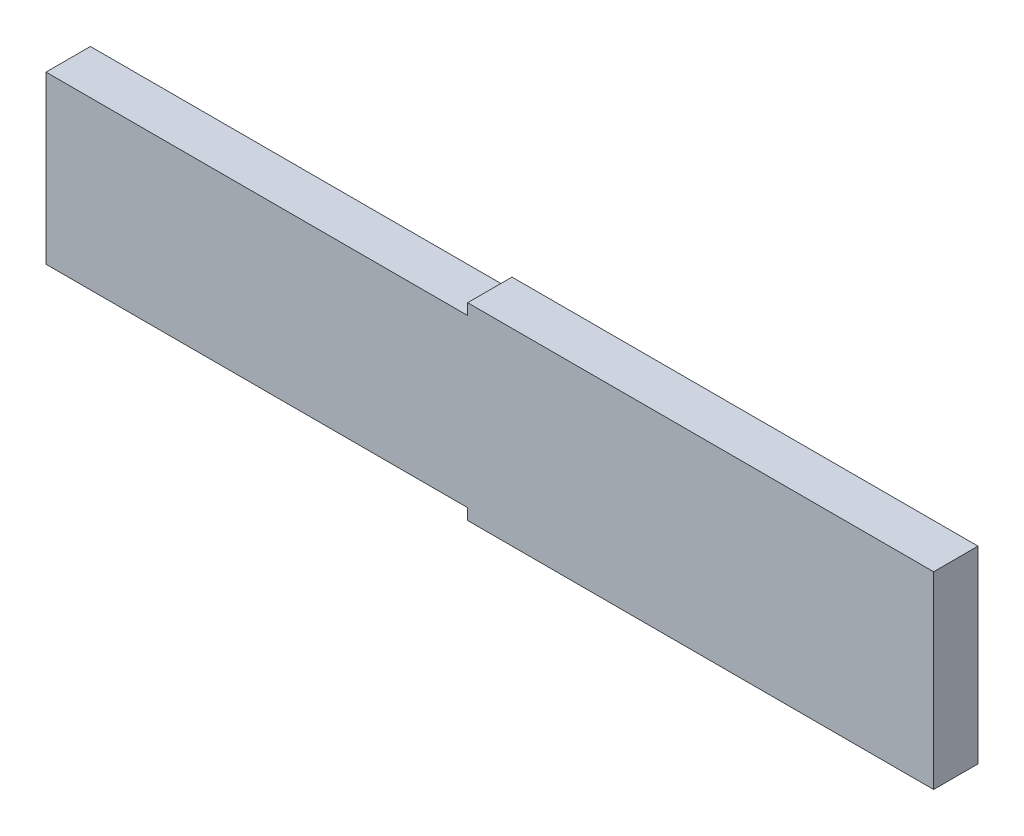
SolidWorks part; units mm, degrees
ref_plane "Ebene vorne" through (0, 0, 0) normal (0, 0, 1) x (1, 0, 0)
ref_plane "Ebene oben" through (0, 0, 0) normal (0, 1, 0) x (1, 0, 0)
ref_plane "Ebene rechts" through (0, 0, 0) normal (1, 0, 0) x (0, 0, -1)
sketch "Skizze1" plane through (0, 0, 0) normal (0, 0, 1) x (1, 0, 0)
  line L0 (-38, -7.5) -> (-38, 7.5)
  line L5 (-38, 7.5) -> (0, 7.5)
  line L6 (0, 7.5) -> (0, 8.5)
  line L7 (0, 8.5) -> (42, 8.5)
  line L8 (42, 8.5) -> (42, -8.5)
  line L10 (0, -8.5) -> (42, -8.5)
  line L11 (0, -7.5) -> (0, -8.5)
  line L12 (-38, -7.5) -> (0, -7.5)
  line L13 (-38, 0) -> (122, 0) construction
  line L14 (0, -12.8676) -> (0, 12.8676) construction
  point P13 (38, 0)
  point P14 (38, 0)
  point P15 (0, 0)
  point P16 (46.1911, 0)
  point P17 (42, 0)
  dimension "D1" = 15
  dimension "D2" = 80
  dimension "D3" = 38
  dimension "D4" = 17
extrude "Aufsatz-Linear austragen1" add sketch "Skizze1" along normal blind 4
